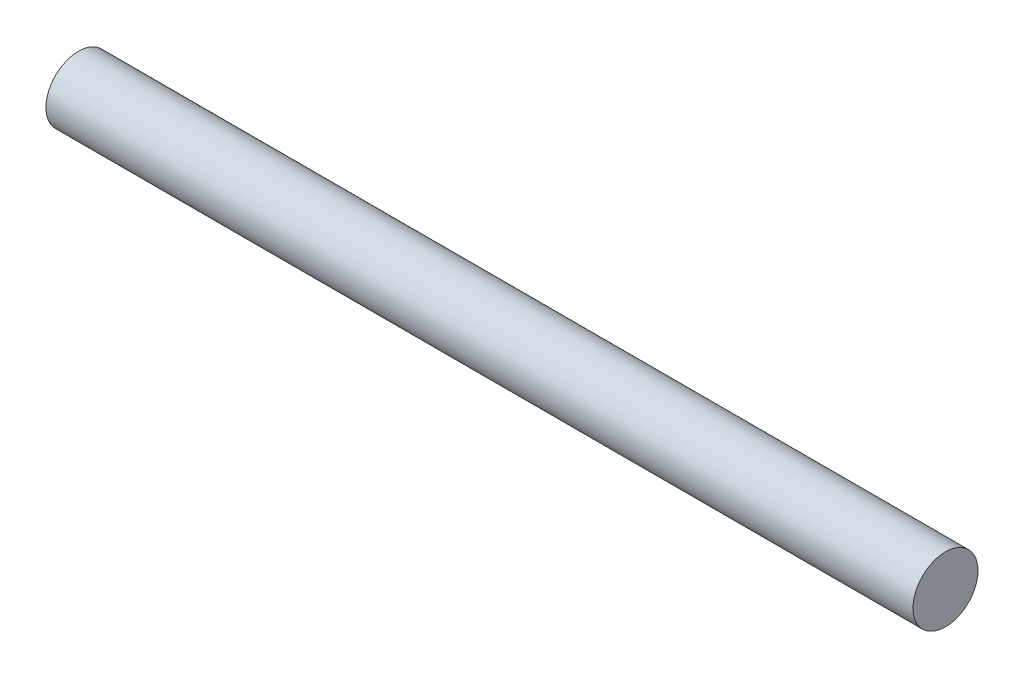
SolidWorks part; units mm, degrees
ref_plane "Front Plane" through (0, 0, 0) normal (0, 0, 1) x (1, 0, 0)
ref_plane "Top Plane" through (0, 0, 0) normal (0, 1, 0) x (1, 0, 0)
ref_plane "Right Plane" through (0, 0, 0) normal (1, 0, 0) x (0, 0, -1)
sketch "Sketch1" plane through (0, 0, 0) normal (1, 0, 0) x (0, 0, -1)
  circle A0 centre (0, 0) radius 1.5
  dimension "D1" = 3
extrude "Boss-Extrude1" add sketch "Sketch1" along normal blind 40
